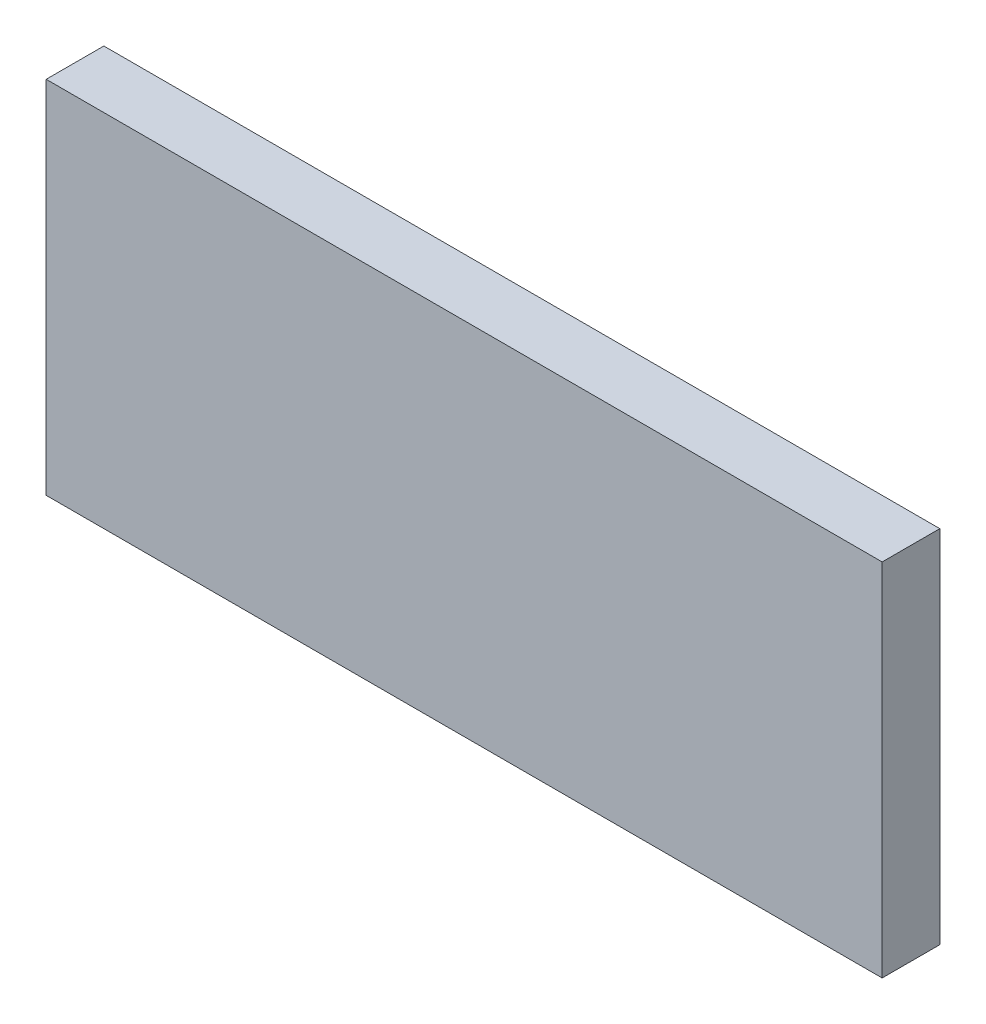
SolidWorks part; units mm, degrees
ref_plane "Front Plane" through (0, 0, 0) normal (0, 0, 1) x (1, 0, 0)
ref_plane "Top Plane" through (0, 0, 0) normal (0, 1, 0) x (1, 0, 0)
ref_plane "Right Plane" through (0, 0, 0) normal (1, 0, 0) x (0, 0, -1)
sketch "Sketch1" plane through (0, 0, 0) normal (0, 0, 1) x (1, 0, 0)
  line L1 (29, -12.5) -> (-29, -12.5)
  line L2 (29, -12.5) -> (29, 12.5)
  line L3 (29, 12.5) -> (-29, 12.5)
  line L4 (-29, -12.5) -> (-29, 12.5)
  line L5 (29, -12.5) -> (-29, 12.5) construction
  line L6 (29, 12.5) -> (-29, -12.5) construction
  point P0 (0, 0)
  dimension "D1" = 25
  dimension "D2" = 58
extrude "Boss-Extrude1" add sketch "Sketch1" along normal blind 4
